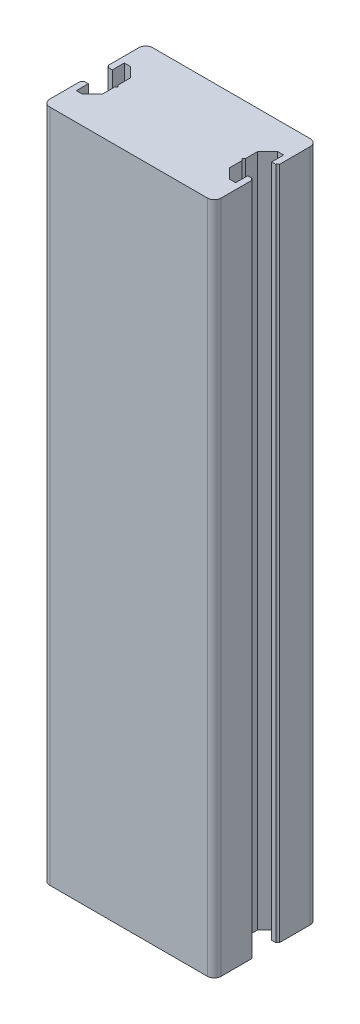
SolidWorks part; units mm, degrees
ref_plane "Front Plane" through (0, 0, 0) normal (0, 0, 1) x (1, 0, 0)
ref_plane "Top Plane" through (0, 0, 0) normal (0, 1, 0) x (1, 0, 0)
ref_plane "Right Plane" through (0, 0, 0) normal (1, 0, 0) x (0, 0, -1)
sketch "Sketch1" plane through (0, 0, 0) normal (0, 1, 0) x (1, 0, 0)
  line L0 (0, 17.25) -> (2.625, 17.25)
  line L5 (0, 0) -> (75, 0)
  line L6 (0, 0) -> (0, 45)
  line L7 (0, 45) -> (75, 45)
  line L8 (75, 0) -> (75, 45)
  line L9 (2.625, 17.25) -> (2.625, 12)
  line L10 (2.625, 12) -> (5.25, 12)
  line L11 (5.25, 12) -> (9.625, 16.375)
  line L12 (9.625, 16.375) -> (9.625, 28.625)
  line L13 (9.625, 28.625) -> (5.25, 33)
  line L14 (5.25, 33) -> (2.625, 33)
  line L15 (2.625, 33) -> (2.625, 27.75)
  line L16 (2.625, 27.75) -> (0, 27.75)
  line L17 (0, 27.75) -> (0, 17.25)
  line L18 (37.5, 45) -> (37.5, 0) construction
  line L19 (72.375, 27.75) -> (75, 27.75)
  line L20 (72.375, 33) -> (72.375, 27.75)
  line L21 (69.75, 33) -> (72.375, 33)
  line L22 (65.375, 28.625) -> (69.75, 33)
  line L23 (65.375, 16.375) -> (65.375, 28.625)
  line L24 (69.75, 12) -> (65.375, 16.375)
  line L25 (72.375, 12) -> (69.75, 12)
  line L26 (72.375, 17.25) -> (72.375, 12)
  line L27 (75, 17.25) -> (72.375, 17.25)
  line L28 (75, 27.75) -> (75, 17.25)
  line L29 (0, 17.25) -> (0.75, 17.25)
  line L30 (0, 16.5) -> (0, 17.25)
  line L31 (0, 27.75) -> (0.75, 27.75)
  line L32 (0, 28.5) -> (0, 27.75)
  line L33 (75, 16.5) -> (75, 17.25)
  line L34 (75, 17.25) -> (74.25, 17.25)
  line L35 (75, 28.5) -> (75, 27.75)
  line L36 (75, 27.75) -> (74.25, 27.75)
  line L37 (9.625, 23.25) -> (10.375, 22.5)
  line L38 (10.375, 22.5) -> (9.625, 21.75)
  line L39 (9.625, 21.75) -> (9.625, 23.25)
  line L40 (64.625, 22.5) -> (65.375, 21.75)
  line L41 (65.375, 23.25) -> (64.625, 22.5)
  line L42 (65.375, 21.75) -> (65.375, 23.25)
  arc A0 (0.75, 27.75) -> (0, 28.5) centre (0, 27.75) ccw
  arc A1 (0.75, 17.25) -> (0, 16.5) centre (0, 17.25) cw
  arc A2 (74.25, 17.25) -> (75, 16.5) centre (75, 17.25) ccw
  arc A3 (74.25, 27.75) -> (75, 28.5) centre (75, 27.75) cw
  point P8 (9.625, 22.5)
  point P17 (0, 22.5)
  dimension "D9" = 0.75
  dimension "D10" = 0.75
  dimension "D1" = 45
  dimension "D2" = 75
  dimension "D3" = 10.5
  dimension "D4" = 12.25
  dimension "D5" = 9.625
  dimension "D6" = 2.625
  dimension "D7" = 2.625
  dimension "D8" = 21
  dimension "D11" = 0.75
  dimension "D12" = 0.75
  dimension "D13" = 0.75
extrude "Boss-Extrude1" add sketch "Sketch1" along normal blind 295 contours L18 L7 L6 A0 L16 L15 L14 L13 L12 L37 L38 L11 L10 L9 L0 A1 L5 | L7 L18 L5 L8 A2 L27 L26 L25 L24 L23 L40 L41 L22 L21 L20 L19 A3
fillet "Fillet1" radius 3 4 edges at (75, 147.5, 0) (0, 147.5, 0) (0, 147.5, -45) (75, 147.5, -45)
sketch "Sketch2" plane through (0, 0, -45) normal (0, 0, -1) x (-1, 0, 0)
  line L0 (-3, 295) -> (-72, 295) construction
  line L1 (-3, 0) -> (-3, 295) construction
  line L2 (-3, 147.5) -> (-72, 147.5) construction
  line L3 (-72, 295) -> (-72, 0) construction
  line L4 (-37.5, 295) -> (-37.5, 0) construction
  line L5 (-3, 0) -> (-72, 0) construction
  circle A0 centre (-6.5, 287) radius 1.5
  circle A1 centre (-6.5, 247) radius 1.5
  circle A2 centre (-6.5, 48) radius 1.5
  circle A3 centre (-6.5, 8) radius 1.5
  circle A4 centre (-68.5, 8) radius 1.5
  circle A5 centre (-68.5, 48) radius 1.5
  circle A6 centre (-68.5, 287) radius 1.5
  circle A7 centre (-68.5, 247) radius 1.5
  dimension "D1" = 3
  dimension "D2" = 40
  dimension "D3" = 8
  dimension "D4" = 3.5
extrude "Cut-Extrude1" cut sketch "Sketch2" against normal blind 10
